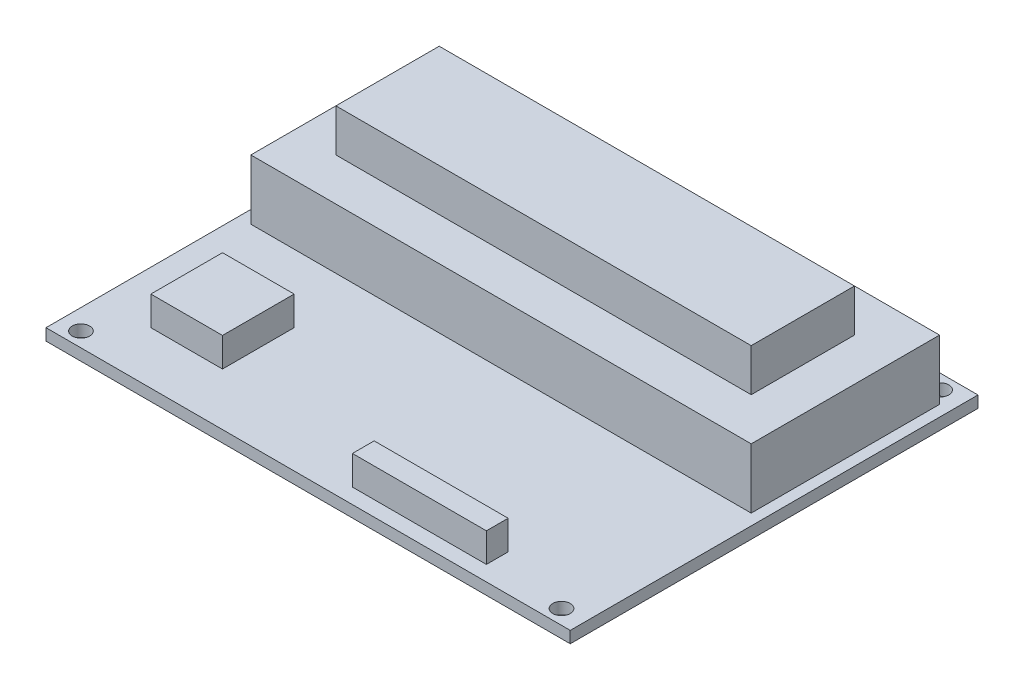
SolidWorks part; units mm, degrees
ref_plane "Front Plane" through (0, 0, 0) normal (0, 0, 1) x (1, 0, 0)
ref_plane "Top Plane" through (0, 0, 0) normal (0, 1, 0) x (1, 0, 0)
ref_plane "Right Plane" through (0, 0, 0) normal (1, 0, 0) x (0, 0, -1)
sketch "Sketch1" plane through (0, 0, 0) normal (0, 1, 0) x (1, 0, 0)
  line L1 (-45, 35) -> (45, 35)
  line L2 (-45, 35) -> (-45, -35)
  line L3 (-45, -35) -> (45, -35)
  line L4 (45, 35) -> (45, -35)
  line L5 (-45, 35) -> (45, -35) construction
  line L6 (-45, -35) -> (45, 35) construction
  point P0 (0, 0)
  dimension "D1" = 90
  dimension "D2" = 70
extrude "Boss-Extrude1" add sketch "Sketch1" along normal blind 2
sketch "Sketch2" plane through (0, 2, 0) normal (0, 1, 0) x (1, 0, 0)
  line L0 (-41.5, 32.5) -> (-41.5, -35) construction
  line L2 (-45, -35) -> (45, -35) construction
  line L3 (-41.5, -32.5) -> (41, -32.5) construction
  line L4 (41, -32.5) -> (41, 32.5) construction
  line L5 (41, 32.5) -> (-41.5, 32.5) construction
  line L6 (-45, 35) -> (-45, -35) construction
  line L7 (45, -35) -> (45, 35) construction
  line L8 (45, 35) -> (-45, 35) construction
  circle A0 centre (-41.5, 32.5) radius 1.5
  circle A1 centre (-41.5, -32.5) radius 1.5
  circle A2 centre (41, -32.5) radius 1.5
  circle A3 centre (41, 32.5) radius 1.5
  dimension "D5" = 3
  dimension "D6" = 3
  dimension "D7" = 3
  dimension "D8" = 3
  dimension "D1" = 3.5
  dimension "D2" = 2.5
  dimension "D3" = 4
  dimension "D4" = 2.5
extrude "Cut-Extrude1" cut sketch "Sketch2" against normal through all
sketch "Sketch3" plane through (0, 2, 0) normal (0, 1, 0) x (1, 0, 0)
  line L0 (45, -35) -> (45, 35) construction
  line L1 (28, -28.6613) -> (5, -28.6613)
  line L2 (28, -28.6613) -> (28, -32.3951)
  line L3 (28, -32.3951) -> (5, -32.3951)
  line L4 (5, -28.6613) -> (5, -32.3951)
  line L5 (-45, -35) -> (45, -35) construction
  line L6 (-36, -13.7) -> (-23.7, -13.7)
  line L7 (-36, -13.7) -> (-36, -26)
  line L8 (-36, -26) -> (-23.7, -26)
  line L9 (-23.7, -13.7) -> (-23.7, -26)
  line L10 (-45, 35) -> (-45, -35) construction
  dimension "D1" = 17
  dimension "D2" = 40
  dimension "D3" = 12.3
  dimension "D4" = 12.3
  dimension "D5" = 9
  dimension "D6" = 9
extrude "Boss-Extrude2" add sketch "Sketch3" along normal blind 5
sketch "Sketch4" plane through (0, 2, 0) normal (0, 1, 0) x (1, 0, 0)
  line L0 (45, 35) -> (-45, 35) construction
  line L1 (-35.5, 23) -> (35.8, 23)
  line L2 (-35.5, 23) -> (-35.5, 5.2648)
  line L3 (-35.5, 5.2648) -> (35.8, 5.2648)
  line L4 (35.8, 23) -> (35.8, 5.2648)
  line L5 (-45, 35) -> (-45, -35) construction
  dimension "D1" = 12
  dimension "D2" = 9.5
  dimension "D3" = 71.3
extrude "Boss-Extrude3" add sketch "Sketch4" along normal blind 17.6
sketch "Sketch5" plane through (0, 2, 0) normal (0, 1, 0) x (1, 0, 0)
  line L0 (-35.5, 23) -> (-35.5, 5.2648) construction
  line L1 (-42.8, 30.3) -> (43.1, 30.3)
  line L2 (-42.8, 30.3) -> (-42.8, -2.0352)
  line L3 (-42.8, -2.0352) -> (43.1, -2.0352)
  line L4 (43.1, 30.3) -> (43.1, -2.0352)
  line L5 (35.8, 23) -> (-35.5, 23) construction
  line L6 (35.8, 5.2648) -> (35.8, 23) construction
  line L7 (-35.5, 5.2648) -> (35.8, 5.2648) construction
  dimension "D1" = 7.3
  dimension "D2" = 7.3
  dimension "D3" = 7.3
  dimension "D4" = 7.3
extrude "Boss-Extrude4" add sketch "Sketch5" along normal blind 10.3
